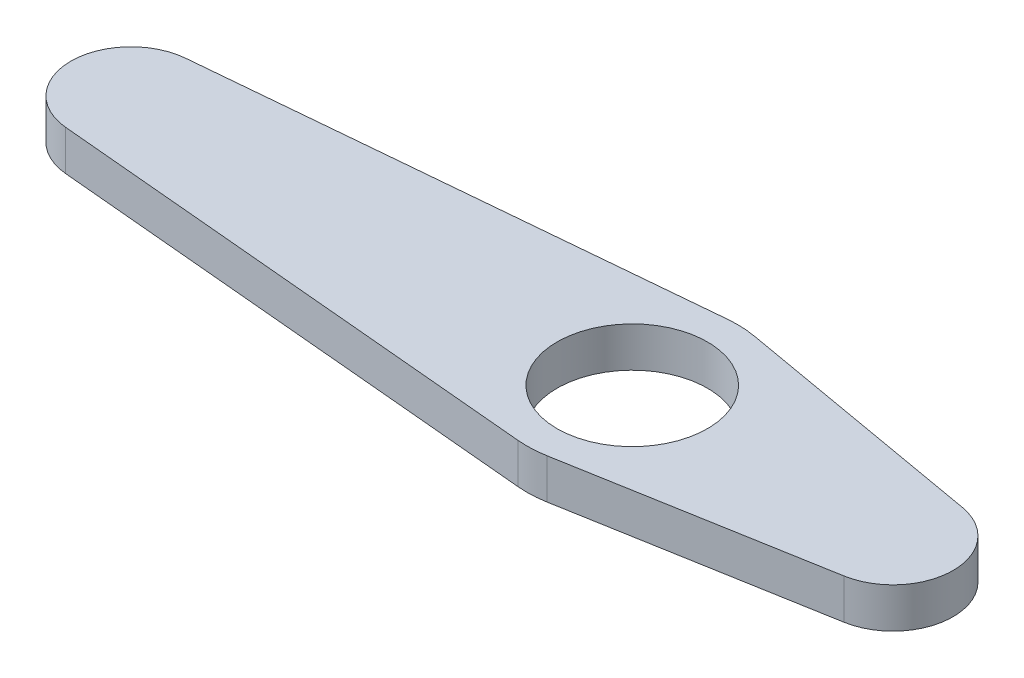
SolidWorks part; units mm, degrees
ref_plane "Front Plane" through (0, 0, 0) normal (0, 0, 1) x (1, 0, 0)
ref_plane "Top Plane" through (0, 0, 0) normal (0, 1, 0) x (1, 0, 0)
ref_plane "Right Plane" through (0, 0, 0) normal (1, 0, 0) x (0, 0, -1)
sketch "Sketch1" plane through (0, 0, 0) normal (0, 1, 0) x (1, 0, 0)
  line L1 (-25.27, -2.9878) -> (-0.4725, -5.2287)
  line L2 (0.9087, 5.1708) -> (13.5192, 2.9547)
  line L3 (0.9087, -5.1708) -> (13.5192, -2.9547)
  line L4 (-0.4725, 5.2287) -> (-25.27, 2.9878)
  circle A0 centre (0, 0) radius 3.75
  arc A3 (13.5192, 2.9547) -> (13.5192, -2.9547) centre (13, 0) cw
  arc A4 (-0.4725, -5.2287) -> (0.9087, -5.1708) centre (0, 0) ccw
  arc A5 (-0.4725, 5.2287) -> (0.9087, 5.1708) centre (0, 0) cw
  circle A6 centre (0, 0) radius 3.5 construction
  arc A10 (-25.27, -2.9878) -> (-25.27, 2.9878) centre (-25, 0) cw
  point P19 (0, 0)
  point P20 (-32.9788, 0)
  point P21 (-24.7606, -4.2584)
  dimension "D1" = 7.5
  dimension "D3" = 7
  dimension "D7" = 1.5
  dimension "D8" = 25
  dimension "D10" = 3
  dimension "D4" = 3
  dimension "D2" = 13
extrude "Boss-Extrude1" add sketch "Sketch1" along normal mid plane 2
